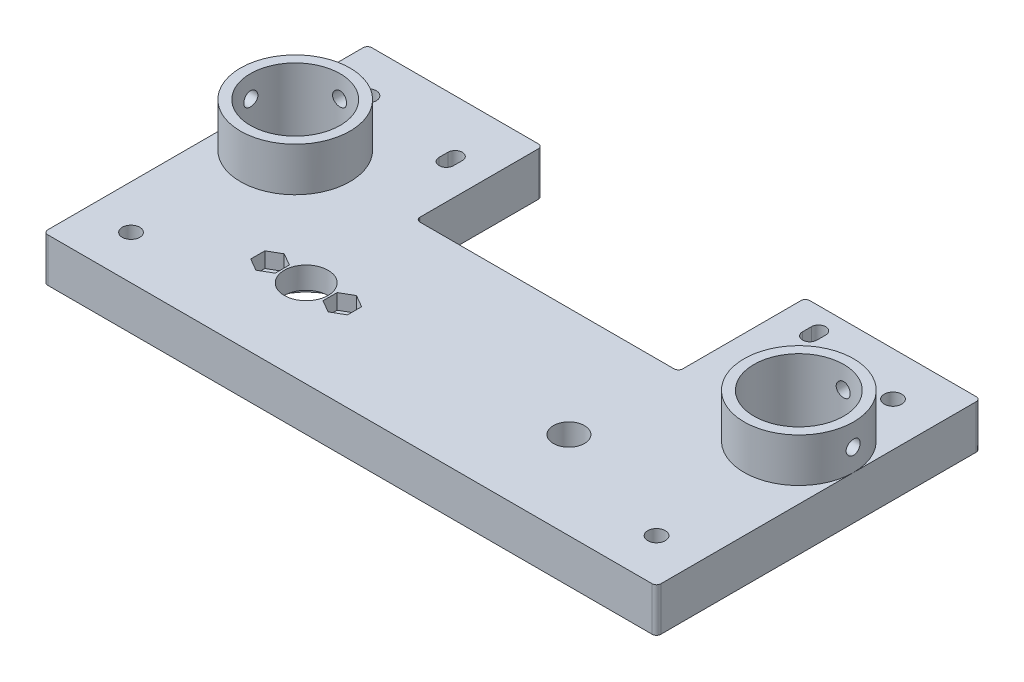
SolidWorks part; units mm, degrees
ref_plane "Alzado" through (0, 0, 0) normal (0, 0, 1) x (1, 0, 0)
ref_plane "Planta" through (0, 0, 0) normal (0, 1, 0) x (1, 0, 0)
ref_plane "Vista lateral" through (0, 0, 0) normal (1, 0, 0) x (0, 0, -1)
sketch "Croquis1" plane through (0, 0, 0) normal (0, 1, 0) x (1, 0, 0)
  line L0 (0, 0) -> (0, 31.359) construction
  line L1 (-45, -22.5) -> (45, -22.5)
  line L2 (-45, -22.5) -> (-45, 22.5)
  line L3 (-45, 22.5) -> (0, 22.5)
  line L4 (45, -22.5) -> (45, 22.5)
  line L5 (-45, -22.5) -> (45, 22.5) construction
  line L6 (-45, 22.5) -> (45, -22.5) construction
  line L11 (0, 22.5) -> (45, 22.5)
  point P0 (0, 0)
  dimension "D1" = 90
  dimension "D2" = 45
extrude "Saliente-Extruir1" add sketch "Croquis1" along normal blind 10
sketch "Croquis3" plane through (0, 10, 0) normal (0, 1, 0) x (1, 0, 0)
  line L0 (0, 0) -> (0, -3.5016) construction
  line L1 (-35, -2.5) -> (-41.5, -2.5) construction
  line L2 (-30, -2.5) -> (-30, 0.3209) construction
  line L3 (45, 22.5) -> (-45, 22.5) construction
  circle A0 centre (-30, -2.5) radius 5
  circle A1 centre (30, -2.5) radius 3.55
  circle A2 centre (-30, -2.5) radius 11.5 construction
  circle A3 centre (-38.25, -2.5) radius 1.6
  circle A4 centre (-21.75, -2.5) radius 1.6
  dimension "D1" = 10
  dimension "D2" = 7.1
  dimension "D4" = 23
  dimension "D5" = 3.2
  dimension "D3" = 60
  dimension "D6" = 25
extrude "Cortar-Extruir1" cut sketch "Croquis3" against normal through all
sketch "Croquis4" plane through (0, 10, 0) normal (0, 1, 0) x (1, 0, 0)
  line L0 (-21.75, -2.5) -> (-38.25, -2.5) construction
  line L1 (-38.25, 0.7332) -> (-41.05, -0.8834)
  line L2 (-41.05, -0.8834) -> (-41.05, -4.1166)
  line L3 (-41.05, -4.1166) -> (-38.25, -5.7332)
  line L4 (-38.25, -5.7332) -> (-35.45, -4.1166)
  line L5 (-35.45, -4.1166) -> (-35.45, -0.8834)
  line L6 (-35.45, -0.8834) -> (-38.25, 0.7332)
  line L7 (-21.75, 0.7332) -> (-24.55, -0.8834)
  line L8 (-24.55, -0.8834) -> (-24.55, -4.1166)
  line L9 (-24.55, -4.1166) -> (-21.75, -5.7332)
  line L10 (-21.75, -5.7332) -> (-18.95, -4.1166)
  line L11 (-18.95, -4.1166) -> (-18.95, -0.8834)
  line L12 (-18.95, -0.8834) -> (-21.75, 0.7332)
  circle A0 centre (-38.25, -2.5) radius 2.8 construction
  circle A1 centre (-21.75, -2.5) radius 2.8 construction
  dimension "D1" = 5.6
extrude "Cortar-Extruir2" cut sketch "Croquis4" against normal blind 3.5
sketch "Croquis5" plane through (0, 0, 0) normal (0, -1, 0) x (1, 0, 0)
  circle A0 centre (-30, 2.5) radius 11.55
  dimension "D1" = 23.1
extrude "Cortar-Extruir3" cut sketch "Croquis5" against normal blind 5
sketch "Croquis6" plane through (0, 10, 0) normal (0, 1, 0) x (1, 0, 0)
  line L0 (-45, -22.5) -> (45, -22.5) construction
  line L3 (-45, 22.5) -> (-45, -22.5) construction
  line L4 (45, -22.5) -> (45, 22.5) construction
  line L5 (0, 0) -> (0, 19.7465) construction
  line L11 (-45, -22.5) -> (45, -22.5)
  line L12 (-45, -22.5) -> (-45, -5.1795)
  line L13 (45, -22.5) -> (45, -5.1795)
  arc A0 (12.6923, -14.5059) -> (-12.6923, -14.5059) centre (0, -22.5) ccw
  arc A2 (12.6923, -14.5059) -> (45, -5.1795) centre (27.5, -5.1795) ccw
  arc A3 (-12.6923, -14.5059) -> (-45, -5.1795) centre (-27.5, -5.1795) cw
  line M22 (45, 22.5) -> (-45, 22.5)
  line M26 (45, 22.5) -> (-45, 22.5)
  line M27 (-45, 22.5) -> (-45, -22.5)
  line M28 (-45, -22.5) -> (45, -22.5)
  line M29 (45, -22.5) -> (45, 22.5)
  dimension "D1" = 30
  dimension "D2" = 17.5
extrude "Cortar-Extruir4" [suppressed] cut sketch "Croquis6" against normal through all contours A3 M28 M26 M27 | A0 A3 L11 A2 | A2 L11 M29 M22
sketch "Croquis8" plane through (0, 10, 0) normal (0, 1, 0) x (1, 0, 0)
  line L1 (45, 22.5) -> (-45, 22.5) construction
  line L2 (-44, 22.5) -> (44, 22.5) construction
  line L7 (-44, 22.5) -> (-44, 51.5) construction
  line L8 (-44, 51.5) -> (44, 51.5) construction
  line L25 (44, 22.5) -> (44, 51.5) construction
  line L26 (0, 0) -> (0, 63.8128) construction
  line L27 (-44, 51.5) -> (-32, 25.5) construction
  line L28 (-44, 51.5) -> (-32, 51.5) construction
  line L29 (-44, 51.5) -> (-44, 25.5) construction
  line L30 (-44, 25.5) -> (-32, 25.5) construction
  line L32 (-32, 51.5) -> (-32, 25.5) construction
  line L33 (44, 51.5) -> (32, 51.5) construction
  line L34 (44, 51.5) -> (44, 39.5) construction
  line L35 (44, 39.5) -> (32, 39.5) construction
  line L36 (32, 51.5) -> (32, 39.5) construction
  line L37 (44, 51.5) -> (32, 39.5) construction
  line L38 (-38, 39.5) -> (-38, 37.5) construction
  line L39 (-36.35, 39.5) -> (-36.35, 37.5)
  line L40 (-39.65, 39.5) -> (-39.65, 37.5)
  line L41 (38, 46.5) -> (38, 44.5) construction
  line L42 (39.65, 46.5) -> (39.65, 44.5)
  line L43 (36.35, 46.5) -> (36.35, 44.5)
  line L45 (-45, 22.5) -> (-30, 22.5)
  line L46 (-45, 22.5) -> (-45, 51.5)
  line L47 (-45, 51.5) -> (-30, 51.5)
  line L48 (-30, 22.5) -> (-30, 51.5)
  line L49 (45, 22.5) -> (30, 22.5)
  line L50 (45, 22.5) -> (45, 51.5)
  line L51 (45, 51.5) -> (30, 51.5)
  line L52 (30, 22.5) -> (30, 51.5)
  arc A9 (-36.35, 39.5) -> (-39.65, 39.5) centre (-38, 39.5) ccw
  arc A10 (-39.65, 37.5) -> (-36.35, 37.5) centre (-38, 37.5) ccw
  arc A11 (39.65, 46.5) -> (36.35, 46.5) centre (38, 46.5) ccw
  arc A12 (36.35, 44.5) -> (39.65, 44.5) centre (38, 44.5) ccw
  point P20 (-38, 38.5)
  point P27 (38, 45.5)
  dimension "D8" = 2
  dimension "D9" = 1.65
  dimension "D1" = 88
  dimension "D2" = 12
  dimension "D3" = 26
  dimension "D4" = 29
  dimension "D5" = 12
  dimension "D6" = 12
  dimension "D10" = 2
  dimension "D11" = 15
  dimension "D12" = 15
extrude "Saliente-Extruir2" add sketch "Croquis8" against normal blind 10
sketch "Croquis9" plane through (0, 0, 0) normal (0, 1, 0) x (1, 0, 0)
  line L0 (-45, 51.5) -> (-45, -22.5) construction
  line L1 (-45, 10) -> (-70, 10)
  line L2 (-45, 10) -> (-45, 35)
  line L3 (-45, 35) -> (-70, 35)
  line L4 (-70, 10) -> (-70, 35)
  line L5 (0, 0) -> (0, 51.5) construction
  line L12 (45, 35) -> (70, 35)
  line L13 (70, 10) -> (70, 35)
  line L14 (45, 10) -> (70, 10)
  line L15 (45, 10) -> (45, 35)
  dimension "D1" = 25
  dimension "D2" = 25
  dimension "D3" = 10
extrude "Saliente-Extruir4" add sketch "Croquis9" along normal blind 10
sketch "Croquis13" plane through (0, 10, 0) normal (0, 1, 0) x (1, 0, 0)
  line L0 (-45, 35) -> (-70, 10) construction
  line L1 (45, 10) -> (70, 35) construction
  line L2 (70, 10) -> (70, 35) construction
  line L3 (-70, 35) -> (-70, 10) construction
  circle A0 centre (-57.5, 22.5) radius 12.5
  circle A1 centre (57.5, 22.5) radius 12.5
extrude "Saliente-Extruir5" add sketch "Croquis13" along normal blind 10
sketch "Croquis15" plane through (0, 20, 0) normal (0, 1, 0) x (1, 0, 0)
  line L1 (0, 0) -> (0, 22.5) construction
  line L2 (-44, 22.5) -> (44, 22.5) construction
  circle A0 centre (-57.5, 22.5) radius 10.25
  circle A1 centre (57.5, 22.5) radius 10.25
  dimension "D1" = 20.5
extrude "Cortar-Extruir5" cut sketch "Croquis15" against normal blind 20
sketch "Croquis16" plane through (0, 0, -35) normal (0, 0, -1) x (-1, 0, 0)
  line L0 (-57.5, 20) -> (-57.5, 10) construction
  line L1 (-45, 20) -> (-70, 20) construction
  line L2 (57.5, 20) -> (57.5, 10) construction
  line L3 (70, 20) -> (45, 20) construction
  circle A0 centre (-57.5, 15) radius 1.6
  circle A1 centre (57.5, 15) radius 1.6
  dimension "D1" = 3.2
extrude "Cortar-Extruir6" cut sketch "Croquis16" against normal blind 10
sketch "Croquis17" plane through (0, 0, 0) normal (0, 1, 0) x (1, 0, 0)
  line L0 (-60, 51.5) -> (-60, 41.5) construction
  line L9 (45, 51.5) -> (70, 51.5)
  line L10 (45, 51.5) -> (45, 35)
  line L11 (45, 35) -> (70, 35)
  line L12 (70, 51.5) -> (70, 35)
  line L13 (70, 10) -> (45, 10)
  line L14 (70, 10) -> (70, -22.5)
  line L15 (70, -22.5) -> (45, -22.5)
  line L16 (45, 10) -> (45, -22.5)
  line L17 (-70, 35) -> (-45, 35)
  line L18 (-70, 35) -> (-70, 51.5)
  line L19 (-70, 51.5) -> (-45, 51.5)
  line L20 (-45, 35) -> (-45, 51.5)
  line L21 (-70, 10) -> (-45, 10)
  line L22 (-70, 10) -> (-70, -22.5)
  line L23 (-70, -22.5) -> (-45, -22.5)
  line L24 (-45, 10) -> (-45, -22.5)
  line L25 (-60, 41.5) -> (-70, 41.5) construction
  line L26 (-60, -22.5) -> (-60, -12.5) construction
  line L27 (-60, -12.5) -> (-70, -12.5) construction
  line L28 (60, -22.5) -> (60, -12.5) construction
  line L29 (60, -12.5) -> (70, -12.5) construction
  line L30 (60, 51.5) -> (60, 41.5) construction
  line L31 (60, 41.5) -> (70, 41.5) construction
  circle A0 centre (-60, 41.5) radius 2
  circle A1 centre (60, 41.5) radius 2
  circle A2 centre (60, -12.5) radius 2
  circle A3 centre (-60, -12.5) radius 2
  dimension "D9" = 4
  dimension "D1" = 10
  dimension "D2" = 10
  dimension "D3" = 10
  dimension "D4" = 10
  dimension "D5" = 10
  dimension "D6" = 10
  dimension "D7" = 10
  dimension "D8" = 10
extrude "Saliente-Extruir6" add sketch "Croquis17" along normal blind 10
fillet "Redondeo1" radius 1 8 edges at (-30, 5, -51.5) (30, 5, -51.5) (30, 5, -22.5) (-30, 5, -22.5) (-70, 5, -51.5) (70, 5, -51.5) (70, 5, 22.5) (-70, 5, 22.5)
sketch "Croquis18" plane through (0, 0, 0) normal (0, -1, 0) x (1, 0, 0)
  line L0 (-44, -51.5) -> (-32, -25.5) construction
  line L1 (-40.8, -44.5) -> (-35.2, -44.5)
  line L2 (-40.8, -44.5) -> (-40.8, -32.5)
  line L3 (-40.8, -32.5) -> (-35.2, -32.5)
  line L4 (-35.2, -44.5) -> (-35.2, -32.5)
  line L5 (-40.8, -44.5) -> (-35.2, -32.5) construction
  line L6 (-40.8, -32.5) -> (-35.2, -44.5) construction
  line L7 (44, -39.5) -> (32, -39.5) construction
  line L8 (35.2, -51.5) -> (40.8, -51.5)
  line L9 (35.2, -51.5) -> (35.2, -39.5)
  line L10 (35.2, -39.5) -> (40.8, -39.5)
  line L11 (40.8, -51.5) -> (40.8, -39.5)
  line L12 (35.2, -51.5) -> (40.8, -39.5) construction
  line L13 (35.2, -39.5) -> (40.8, -51.5) construction
  point P0 (-38, -38.5)
  point P7 (38, -45.5)
  dimension "D1" = 5.6
  dimension "D2" = 12
  dimension "D3" = 5.6
extrude "Cortar-Extruir7" cut sketch "Croquis18" against normal blind 3
sketch "Croquis19" plane through (0, 0, 0) normal (1, 0, 0) x (0, 0, -1)
  line L0 (22.5, 20) -> (22.5, 10) construction
  line L1 (35, 20) -> (10, 20) construction
  circle A0 centre (22.5, 15) radius 1.6
  dimension "D1" = 3.2
extrude "Cortar-Extruir10" cut sketch "Croquis19" along normal through all from offset 60
mirror "Simetría1" about plane through (0, 0, 0) normal (1, 0, 0) of "Cortar-Extruir10"
